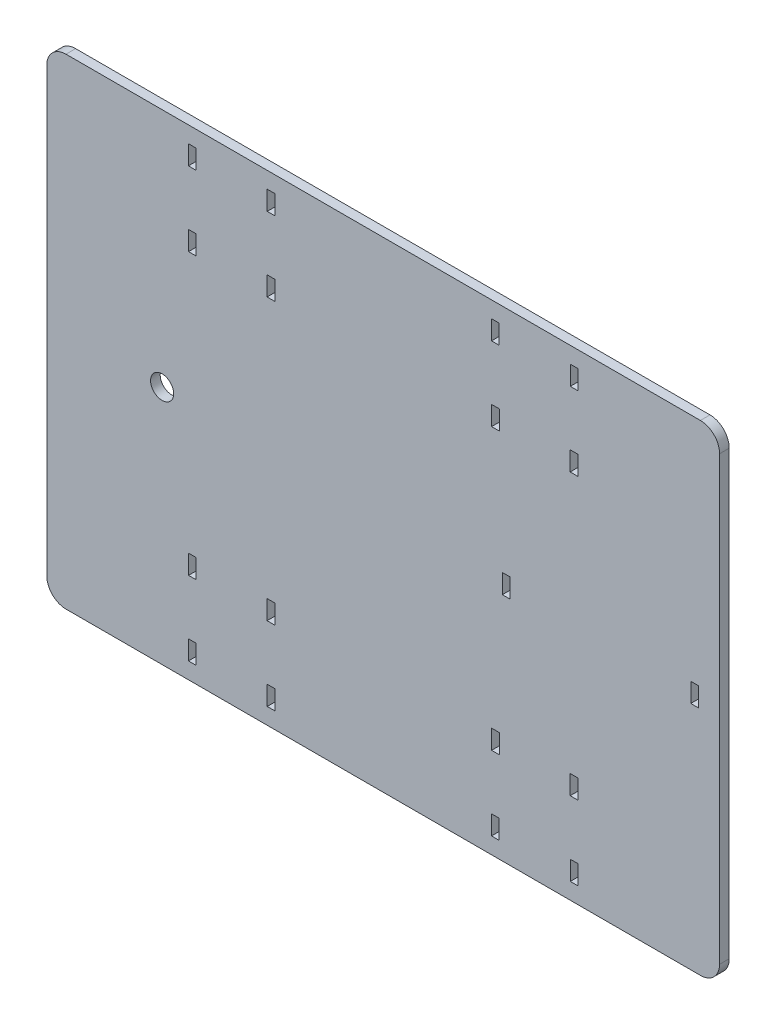
SolidWorks part; units mm, degrees
material "Acrylic (Medium-high impact)"
ref_plane "Front Plane" through (0, 0, 0) normal (0, 0, 1) x (1, 0, 0)
ref_plane "Top Plane" through (0, 0, 0) normal (0, 1, 0) x (1, 0, 0)
ref_plane "Right Plane" through (0, 0, 0) normal (1, 0, 0) x (0, 0, -1)
sketch "Sketch1" plane through (0, 0, 0) normal (0, 0, 1) x (1, 0, 0)
  line L1 (-165, 125) -> (165, 125)
  line L2 (-175, 115) -> (-175, -115)
  line L3 (-165, -125) -> (165, -125)
  line L4 (175, 115) -> (175, -115)
  line L5 (-175, 125) -> (175, -125) construction
  line L6 (-175, -125) -> (175, 125) construction
  arc A0 (-175, -115) -> (-165, -125) centre (-165, -115) ccw
  arc A1 (165, -125) -> (175, -115) centre (165, -115) ccw
  arc A2 (-165, 125) -> (-175, 115) centre (-165, 115) ccw
  arc A3 (165, 125) -> (175, 115) centre (165, 115) cw
  point P0 (0, 0)
  dimension "D3" = 10
  dimension "D1" = 250
  dimension "D2" = 350
extrude "Boss-Extrude1" add sketch "Sketch1" along normal blind 5
sketch "Sketch2" plane through (0, 0, 5) normal (0, 0, 1) x (1, 0, 0)
  line L0 (97.3285, 102) -> (97.3285, 125) construction
  line L1 (97.3285, 116.512) -> (101.3285, 116.512)
  line L2 (97.3285, 116.512) -> (97.3285, 106.512)
  line L3 (97.3285, 106.512) -> (101.3285, 106.512)
  line L4 (101.3285, 116.512) -> (101.3285, 106.512)
  line L5 (78.8285, 125) -> (78.8285, 25.5392) construction
  line L6 (97.2625, 77.9175) -> (101.2625, 77.9175)
  line L7 (97.2625, 77.9175) -> (97.2625, 67.9175)
  line L8 (97.2625, 67.9175) -> (101.2625, 67.9175)
  line L9 (101.2625, 77.9175) -> (101.2625, 67.9175)
  line L10 (97.3285, 125) -> (60.3285, 125) construction
  line L11 (60.3945, 77.9175) -> (60.3945, 67.9175)
  line L12 (60.3945, 67.9175) -> (56.3945, 67.9175)
  line L13 (56.3945, 77.9175) -> (56.3945, 67.9175)
  line L14 (60.3945, 77.9175) -> (56.3945, 77.9175)
  line L15 (60.3285, 116.512) -> (60.3285, 106.512)
  line L16 (60.3285, 106.512) -> (56.3285, 106.512)
  line L17 (56.3285, 116.512) -> (56.3285, 106.512)
  line L18 (60.3285, 116.512) -> (56.3285, 116.512)
  line L19 (175, 0) -> (-242.622, 0) construction
  line L20 (175, -115) -> (175, 115) construction
  line L21 (0, 0) -> (0, 208.4187) construction
  line L22 (78.8285, -125) -> (78.8285, -25.5392) construction
  line L23 (60.3285, -116.512) -> (56.3285, -116.512)
  line L24 (56.3285, -116.512) -> (56.3285, -106.512)
  line L25 (60.3285, -106.512) -> (56.3285, -106.512)
  line L26 (60.3285, -116.512) -> (60.3285, -106.512)
  line L27 (60.3945, -77.9175) -> (56.3945, -77.9175)
  line L28 (56.3945, -77.9175) -> (56.3945, -67.9175)
  line L29 (60.3945, -67.9175) -> (56.3945, -67.9175)
  line L30 (60.3945, -77.9175) -> (60.3945, -67.9175)
  line L31 (101.2625, -77.9175) -> (101.2625, -67.9175)
  line L32 (97.2625, -67.9175) -> (101.2625, -67.9175)
  line L33 (97.2625, -77.9175) -> (97.2625, -67.9175)
  line L34 (97.2625, -77.9175) -> (101.2625, -77.9175)
  line L35 (101.3285, -116.512) -> (101.3285, -106.512)
  line L36 (97.3285, -106.512) -> (101.3285, -106.512)
  line L37 (97.3285, -116.512) -> (97.3285, -106.512)
  line L38 (97.3285, -116.512) -> (101.3285, -116.512)
  line L39 (-78.8285, -125) -> (-78.8285, -25.5392) construction
  line L40 (-175, 0) -> (242.622, 0) construction
  line L41 (-78.8285, 125) -> (-78.8285, 25.5392) construction
  line L42 (-97.3285, -116.512) -> (-101.3285, -116.512)
  line L43 (-97.3285, -116.512) -> (-97.3285, -106.512)
  line L44 (-97.3285, -106.512) -> (-101.3285, -106.512)
  line L45 (-101.3285, -116.512) -> (-101.3285, -106.512)
  line L46 (-97.2625, -77.9175) -> (-101.2625, -77.9175)
  line L47 (-97.2625, -77.9175) -> (-97.2625, -67.9175)
  line L48 (-97.2625, -67.9175) -> (-101.2625, -67.9175)
  line L49 (-101.2625, -77.9175) -> (-101.2625, -67.9175)
  line L50 (-60.3945, -77.9175) -> (-60.3945, -67.9175)
  line L51 (-60.3945, -67.9175) -> (-56.3945, -67.9175)
  line L52 (-56.3945, -77.9175) -> (-56.3945, -67.9175)
  line L53 (-60.3945, -77.9175) -> (-56.3945, -77.9175)
  line L54 (-60.3285, -116.512) -> (-60.3285, -106.512)
  line L55 (-60.3285, -106.512) -> (-56.3285, -106.512)
  line L56 (-56.3285, -116.512) -> (-56.3285, -106.512)
  line L57 (-60.3285, -116.512) -> (-56.3285, -116.512)
  line L58 (-60.3285, 116.512) -> (-56.3285, 116.512)
  line L59 (-56.3285, 116.512) -> (-56.3285, 106.512)
  line L60 (-60.3285, 106.512) -> (-56.3285, 106.512)
  line L61 (-60.3285, 116.512) -> (-60.3285, 106.512)
  line L62 (-60.3945, 77.9175) -> (-56.3945, 77.9175)
  line L63 (-56.3945, 77.9175) -> (-56.3945, 67.9175)
  line L64 (-60.3945, 67.9175) -> (-56.3945, 67.9175)
  line L65 (-60.3945, 77.9175) -> (-60.3945, 67.9175)
  line L66 (-101.2625, 77.9175) -> (-101.2625, 67.9175)
  line L67 (-97.2625, 67.9175) -> (-101.2625, 67.9175)
  line L68 (-97.2625, 77.9175) -> (-97.2625, 67.9175)
  line L69 (-97.2625, 77.9175) -> (-101.2625, 77.9175)
  line L70 (-101.3285, 116.512) -> (-101.3285, 106.512)
  line L71 (-97.3285, 106.512) -> (-101.3285, 106.512)
  line L72 (-97.3285, 116.512) -> (-97.3285, 106.512)
  line L73 (-97.3285, 116.512) -> (-101.3285, 116.512)
  dimension "D1" = 4
  dimension "D2" = 10
  dimension "D3" = 4
  dimension "D4" = 10
extrude "Cut-Extrude1" cut sketch "Sketch2" against normal blind 10
sketch "Sketch3" plane through (0, 0, 5) normal (0, 0, 1) x (1, 0, 0)
  line L0 (175, 0) -> (97.2316, 0) construction
  line L1 (160, -5) -> (164, -5)
  line L2 (160, -5) -> (160, 5)
  line L3 (160, 5) -> (164, 5)
  line L4 (164, -5) -> (164, 5)
  line L5 (175, -115) -> (175, 115) construction
  line L6 (-175, 115) -> (-175, -115) construction
  line L7 (66, 5) -> (62, 5)
  line L8 (66, 5) -> (66, -5)
  line L9 (66, -5) -> (62, -5)
  line L10 (62, 5) -> (62, -5)
  line L11 (-165, -125) -> (165, -125) construction
  circle A0 centre (-115, 0) radius 6
  point P9 (164, 0)
  point P14 (66, 0)
  point P17 (-175, 0)
  dimension "D8" = 12
  dimension "D1" = 15
  dimension "D2" = 4
  dimension "D3" = 10
  dimension "D4" = 4
  dimension "D5" = 10
  dimension "D6" = 109
  dimension "D7" = 60
  dimension "D9" = 125
extrude "Cut-Extrude2" cut sketch "Sketch3" against normal blind 10
